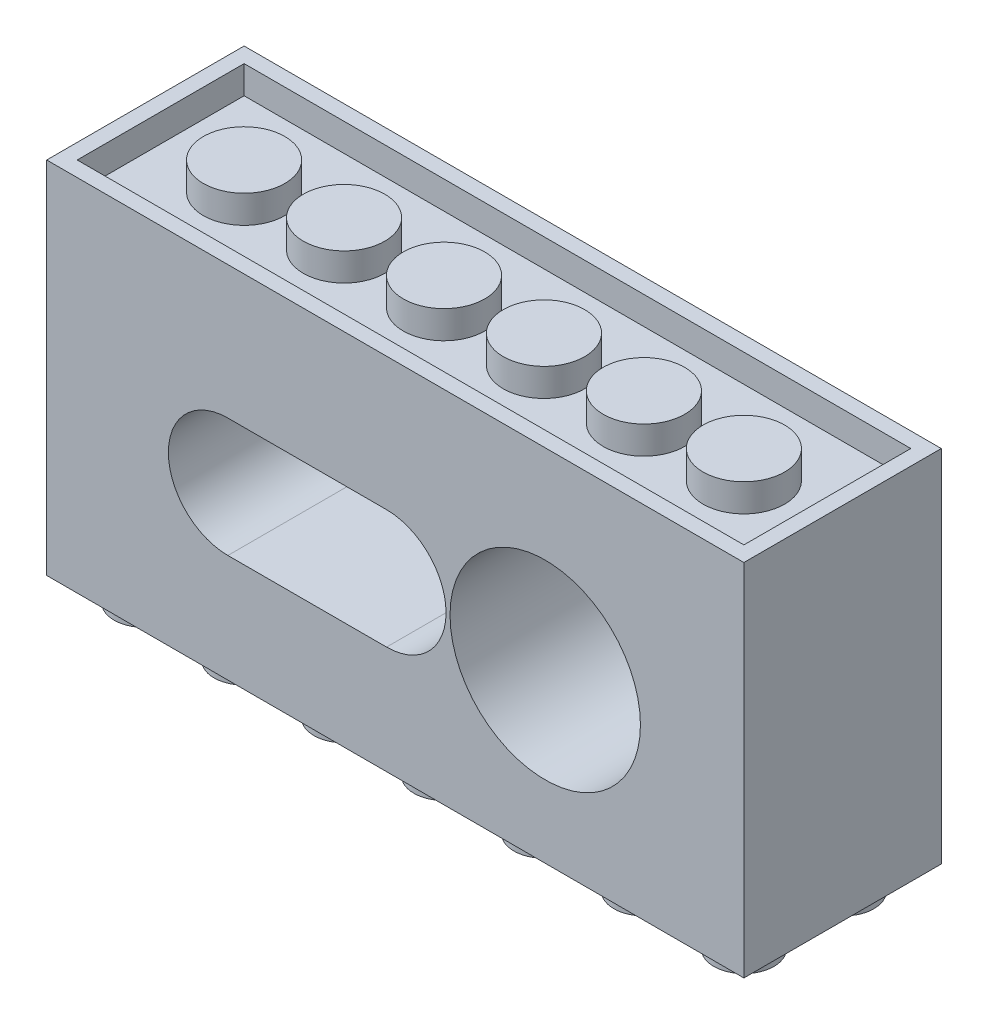
SolidWorks part; units mm, degrees
ref_plane "Front Plane" through (0, 0, 0) normal (0, 0, 1) x (1, 0, 0)
ref_plane "Top Plane" through (0, 0, 0) normal (0, 1, 0) x (1, 0, 0)
ref_plane "Right Plane" through (0, 0, 0) normal (1, 0, 0) x (0, 0, -1)
sketch "Sketch1" plane through (0, 0, 0) normal (0, 1, 0) x (1, 0, 0)
  line L1 (-39.0999, 16.0935) -> (16.7001, 16.0935)
  line L2 (-39.0999, 16.0935) -> (-39.0999, 0.2935)
  line L3 (-39.0999, 0.2935) -> (16.7001, 0.2935)
  line L4 (16.7001, 16.0935) -> (16.7001, 0.2935)
  dimension "D1" = 55.8
  dimension "D2" = 15.8
extrude "Boss-Extrude1" add sketch "Sketch1" along normal blind 28.8
sketch "Sketch2" plane through (0, 0, -0.2935) normal (0, 0, 1) x (1, 0, 0)
  line L0 (-39.0999, 0) -> (16.7001, 0) construction
  line L1 (-11.8999, 13.4) -> (-24.5999, 13.4) construction
  line L2 (-11.8999, 8.6375) -> (-24.5999, 8.6375)
  line L3 (-11.8999, 18.1625) -> (-24.5999, 18.1625)
  line L4 (16.7001, 28.8) -> (16.7001, 0) construction
  circle A0 centre (0.8001, 13.4) radius 7.62
  arc A1 (-11.8999, 8.6375) -> (-11.8999, 18.1625) centre (-11.8999, 13.4) ccw
  arc A2 (-24.5999, 18.1625) -> (-24.5999, 8.6375) centre (-24.5999, 13.4) ccw
  point P6 (-18.2499, 13.4)
  dimension "D4" = 15.24
  dimension "D5" = 4.7625
  dimension "D1" = 13.4
  dimension "D2" = 12.7
  dimension "D3" = 12.7
  dimension "D6" = 15.9
extrude "Cut-Extrude1" cut sketch "Sketch2" against normal blind 12.7
sketch "Sketch4" plane through (0, 0, -16.0935) normal (0, 0, -1) x (-1, 0, 0)
  line L0 (-16.7001, 28.8) -> (-16.7001, 0) construction
  line L1 (-16.7001, 28.8) -> (39.0999, 28.8) construction
  circle A6 centre (-0.8001, 13.4) radius 2.7781
  circle A7 centre (11.8999, 13.4) radius 1.8415
  circle A8 centre (24.5999, 13.4) radius 1.8415
  dimension "D1" = 5.5563
  dimension "D2" = 3.683
  dimension "D3" = 3.683
  dimension "D4" = 12.7
  dimension "D5" = 12.7
  dimension "D6" = 15.9
  dimension "D7" = 15.4
extrude "Cut-Extrude2" cut sketch "Sketch4" against normal blind 12.7
sketch "Sketch5" plane through (0, 0, -16.0935) normal (0, 0, -1) x (-1, 0, 0)
  line L2 (24.5999, 18.1625) -> (11.8999, 18.1625)
  line L3 (11.8999, 8.6375) -> (24.5999, 8.6375)
  line L12 (24.5999, 18.1625) -> (11.8999, 18.1625)
  line L13 (11.8999, 8.6375) -> (24.5999, 8.6375)
  arc A2 (11.8999, 18.1625) -> (11.8999, 8.6375) centre (11.8999, 13.4) ccw
  arc A3 (24.5999, 8.6375) -> (24.5999, 18.1625) centre (24.5999, 13.4) ccw
  arc A4 (11.8999, 18.1625) -> (11.8999, 8.6375) centre (11.8999, 13.4) ccw
  arc A5 (24.5999, 8.6375) -> (24.5999, 18.1625) centre (24.5999, 13.4) ccw
  dimension "D2" = 0
extrude "Cut-Extrude6" cut sketch "Sketch5" against normal blind 1.905
sketch "Sketch8" plane through (0, 28.8, 0) normal (0, 1, 0) x (1, 0, 0)
  line L0 (-39.0999, 16.0935) -> (-39.0999, 0.2935) construction
  line L1 (-37.8799, 14.8735) -> (15.4801, 14.8735)
  line L2 (-37.8799, 14.8735) -> (-37.8799, 1.5135)
  line L3 (-37.8799, 1.5135) -> (15.4801, 1.5135)
  line L4 (15.4801, 14.8735) -> (15.4801, 1.5135)
  line L9 (16.7001, 16.0935) -> (-39.0999, 16.0935) construction
  line L10 (-39.0999, 0.2935) -> (16.7001, 0.2935) construction
  line L11 (16.7001, 0.2935) -> (16.7001, 16.0935) construction
  line L12 (-39.0999, 16.0935) -> (-39.0999, 0.2935) construction
  circle A0 centre (-31.1999, 8.1935) radius 3.26
  circle A1 centre (-23.1999, 8.1935) radius 3.26
  circle A2 centre (-15.1999, 8.1935) radius 3.26
  circle A3 centre (-7.1999, 8.1935) radius 3.26
  circle A4 centre (0.8001, 8.1935) radius 3.26
  circle A5 centre (8.8001, 8.1935) radius 3.26
  point P14 (-39.0999, 8.1935)
  dimension "D1" = 6.52
  dimension "D2" = 1.22
  dimension "D3" = 1.22
  dimension "D4" = 1.22
  dimension "D5" = 1.22
  dimension "D6" = 7.9
  dimension "D7" = 7.9
  dimension "D8" = 6
extrude "Cut-Extrude8" cut sketch "Sketch8" against normal blind 2.23
sketch "Sketch11" plane through (0, 0, 0) normal (0, -1, 0) x (1, 0, 0)
  line L1 (-39.0999, -0.2935) -> (16.7001, -0.2935) construction
  line L2 (-39.0999, -16.0935) -> (-39.0999, -0.2935) construction
  circle A0 centre (-35.1999, -4.1935) radius 2.405
  circle A1 centre (-35.1999, -12.1935) radius 2.405
  circle A2 centre (-27.1999, -4.1935) radius 2.405
  circle A3 centre (-27.1999, -12.1935) radius 2.405
  circle A4 centre (-19.1999, -4.1935) radius 2.405
  circle A5 centre (-19.1999, -12.1935) radius 2.405
  circle A6 centre (-11.1999, -4.1935) radius 2.405
  circle A7 centre (-11.1999, -12.1935) radius 2.405
  circle A8 centre (-3.1999, -4.1935) radius 2.405
  circle A9 centre (-3.1999, -12.1935) radius 2.405
  circle A10 centre (4.8001, -4.1935) radius 2.405
  circle A11 centre (4.8001, -12.1935) radius 2.405
  circle A12 centre (12.8001, -4.1935) radius 2.405
  circle A13 centre (12.8001, -12.1935) radius 2.405
  dimension "D1" = 4.81
  dimension "D2" = 4.81
  dimension "D3" = 8
  dimension "D4" = 3.9
  dimension "D5" = 3.9
  dimension "D6" = 3.9
  dimension "D7" = 7
extrude "Boss-Extrude3" add sketch "Sketch11" along normal blind 1.9
